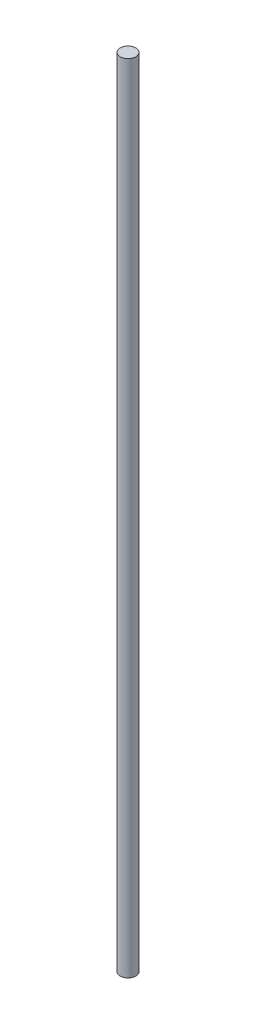
SolidWorks part; units mm, degrees
material "ABS PC"
ref_plane "Front Plane" through (0, 0, 0) normal (0, 0, 1) x (1, 0, 0)
ref_plane "Top Plane" through (0, 0, 0) normal (0, 1, 0) x (1, 0, 0)
ref_plane "Right Plane" through (0, 0, 0) normal (1, 0, 0) x (0, 0, -1)
sketch "Sketch1" plane through (0, 0, 0) normal (0, 1, 0) x (1, 0, 0)
  circle A0 centre (0, 0) radius 0.875
extrude "Boss-Extrude1" add sketch "Sketch1" along normal blind 90
